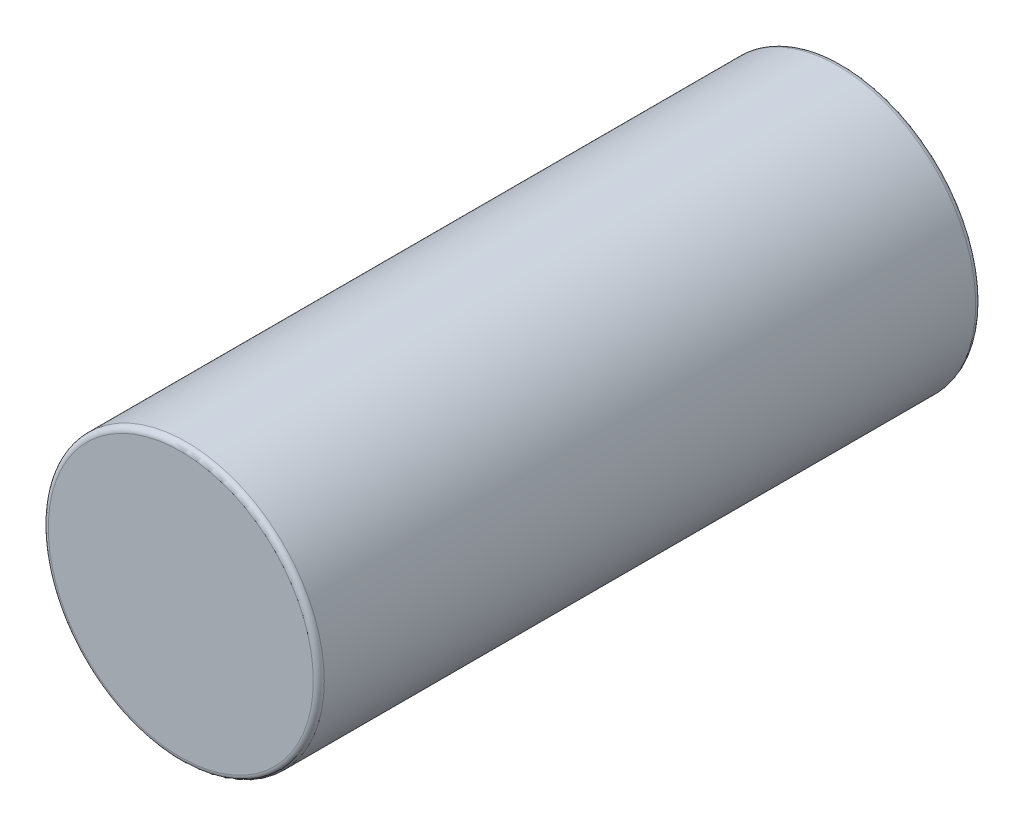
SolidWorks part; units mm, degrees
material "Plain Carbon Steel"
ref_plane "Front Plane" through (0, 0, 0) normal (0, 0, 1) x (1, 0, 0)
ref_plane "Top Plane" through (0, 0, 0) normal (0, 1, 0) x (1, 0, 0)
ref_plane "Right Plane" through (0, 0, 0) normal (1, 0, 0) x (0, 0, -1)
sketch "Sketch1" plane through (0, 0, 0) normal (0, 0, 1) x (1, 0, 0)
  circle A0 centre (0, 0) radius 2.5
  dimension "D1" = 5
extrude "Boss-Extrude1" add sketch "Sketch1" against normal blind 12
fillet "Fillet1" radius 0.1 2 edges at (2.5, 0, -12) (2.5, 0, 0)
